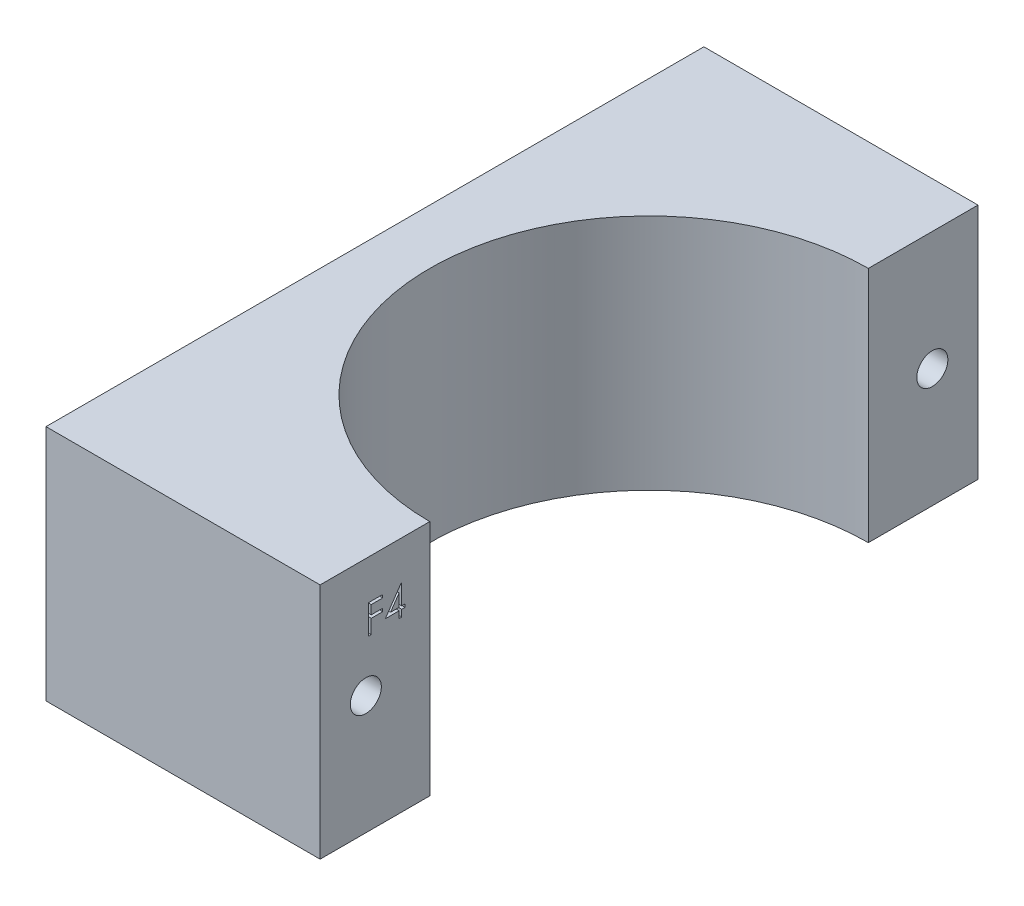
SolidWorks part; units mm, degrees
ref_plane "Front Plane" through (0, 0, 0) normal (0, 0, 1) x (1, 0, 0)
ref_plane "Top Plane" through (0, 0, 0) normal (0, 1, 0) x (1, 0, 0)
ref_plane "Right Plane" through (0, 0, 0) normal (1, 0, 0) x (0, 0, -1)
sketch "Sketch1" plane through (0, 0, 0) normal (0, 1, 0) x (1, 0, 0)
  line L0 (-46.9983, 32.5286) -> (-46.9983, -39.4714)
  line L1 (-46.9983, -39.4714) -> (-16.9983, -39.4714)
  line L2 (-16.9983, -39.4714) -> (-16.9983, -27.4714)
  line L3 (-46.9983, 32.5286) -> (-16.9983, 32.5286)
  line L4 (-16.9983, 32.5286) -> (-16.9983, 20.5286)
  arc A0 (-16.9983, 20.5286) -> (-16.9983, -27.4714) centre (-16.9983, -3.4714) ccw
  dimension "D1" = 72
  dimension "D2" = 30
  dimension "D3" = 30
  dimension "D4" = 12
  dimension "D5" = 12
extrude "Boss-Extrude1" add sketch "Sketch1" along normal blind 26
sketch "Sketch2" plane through (-16.9983, 0, 0) normal (1, 0, 0) x (0, 0, -1)
  line L0 (-34.4714, 26) -> (-34.4714, 0) construction
  line L1 (-39.4714, 26) -> (-27.4714, 26) construction
  line L2 (-39.4714, 0) -> (-27.4714, 0) construction
  line L3 (27.5286, 26) -> (27.5286, 0) construction
  line L4 (20.5286, 26) -> (32.5286, 26) construction
  line L5 (20.5286, 0) -> (32.5286, 0) construction
  line L6 (-39.4714, 26) -> (-39.4714, 0) construction
  line L7 (32.5286, 26) -> (32.5286, 0) construction
  circle A0 centre (-34.4714, 13) radius 1.7
  circle A1 centre (27.5286, 13) radius 1.7
  dimension "D1" = 5
  dimension "D2" = 5
extrude "Cut-Extrude1" cut sketch "Sketch2" against normal through all
sketch "Sketch3" plane through (-16.9983, 0, 0) normal (1, 0, 0) x (0, 0, -1)
  text T0 "F4"
extrude "Cut-Extrude2" cut sketch "Sketch3" against normal blind 1
